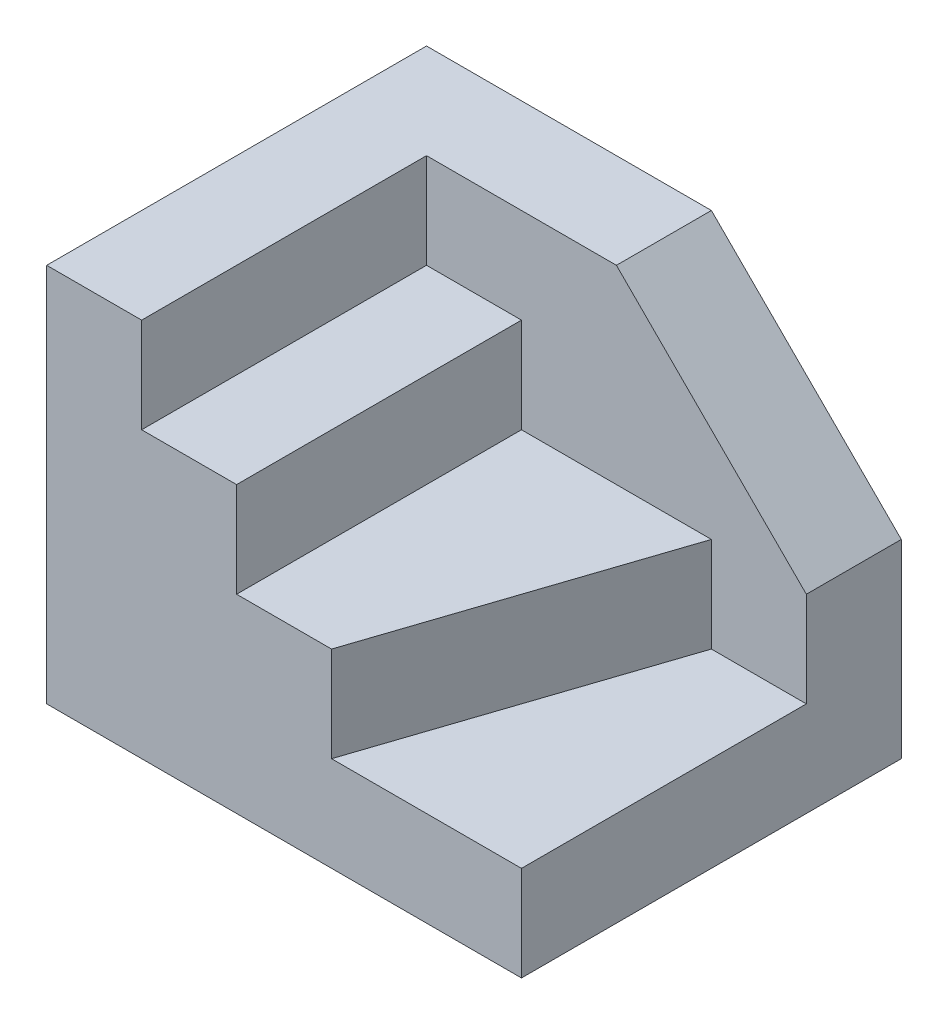
SolidWorks part; units mm, degrees
ref_plane "前基準面" through (0, 0, 0) normal (0, 0, 1) x (1, 0, 0)
ref_plane "上基準面" through (0, 0, 0) normal (0, 1, 0) x (1, 0, 0)
ref_plane "右基準面" through (0, 0, 0) normal (1, 0, 0) x (0, 0, -1)
sketch "草圖1" plane through (0, 0, 0) normal (0, 1, 0) x (1, 0, 0)
  line L1 (-25, -20) -> (25, -20)
  line L2 (-25, -20) -> (-25, 20)
  line L3 (-25, 20) -> (25, 20)
  line L4 (25, -20) -> (25, 20)
  line L5 (-25, -20) -> (25, 20) construction
  line L6 (-25, 20) -> (25, -20) construction
  point P0 (0, 0)
  dimension "D1" = 40
  dimension "D2" = 50
extrude "填料-伸長1" add sketch "草圖1" along normal blind 40
sketch "草圖2" plane through (0, 0, 20) normal (0, 0, 1) x (1, 0, 0)
  line L0 (-15, 40) -> (-15, 30)
  line L1 (-25, 40) -> (25, 40) construction
  line L2 (-15, 30) -> (-5, 30)
  line L3 (-5, 30) -> (-5, 20)
  line L4 (-5, 20) -> (5, 20)
  line L5 (5, 20) -> (5, 10)
  line L6 (5, 10) -> (25, 10)
  line L7 (25, 40) -> (25, 0) construction
  line L8 (25, 10) -> (25, 40)
  line L9 (25, 40) -> (-15, 40)
  line L11 (-25, 40) -> (-25, 0) construction
  dimension "D1" = 10
  dimension "D2" = 10
  dimension "D3" = 10
  dimension "D4" = 20
  dimension "D5" = 10
  dimension "D6" = 10
extrude "除料-伸長1" cut sketch "草圖2" against normal blind 30
sketch "草圖3" plane through (0, 10, 0) normal (0, 1, 0) x (1, 0, 0)
  line L0 (5, -20) -> (15, 10)
  line L1 (5, 10) -> (25, 10) construction
  line L2 (15, 10) -> (5, 10)
  line L3 (25, 10) -> (-15, 10) construction
  line L4 (5, 10) -> (5, -20)
  dimension "D1" = 10
extrude "填料-伸長2" add sketch "草圖3" along normal blind 10
sketch "草圖4" plane through (0, 0, -10) normal (0, 0, 1) x (1, 0, 0)
  line L0 (5, 40) -> (25, 20)
  line L1 (25, 40) -> (-15, 40) construction
  line L2 (25, 10) -> (25, 40) construction
  line L3 (25, 20) -> (25, 40)
  line L4 (25, 40) -> (5, 40)
  dimension "D1" = 20
  dimension "D2" = 20
extrude "除料-伸長2" cut sketch "草圖4" against normal through all
